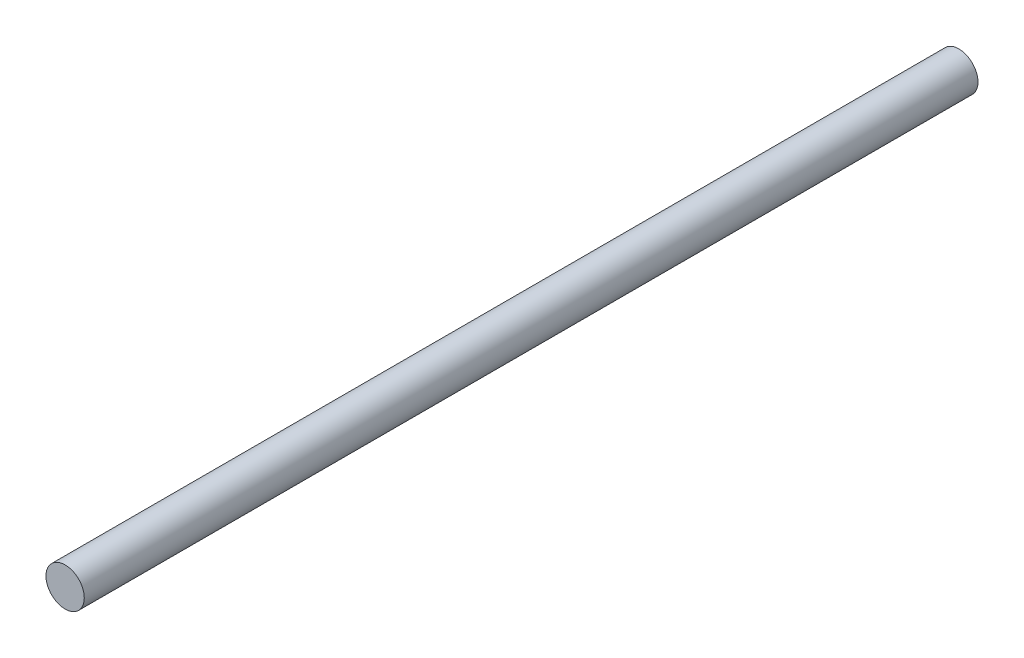
SolidWorks part; units mm, degrees
material "Plain Carbon Steel"
ref_plane "Front Plane" through (0, 0, 0) normal (0, 0, 1) x (1, 0, 0)
ref_plane "Top Plane" through (0, 0, 0) normal (0, 1, 0) x (1, 0, 0)
ref_plane "Right Plane" through (0, 0, 0) normal (1, 0, 0) x (0, 0, -1)
sketch "Sketch1" plane through (0, 0, 0) normal (0, 0, 1) x (1, 0, 0)
  circle A0 centre (0, 0) radius 1.5
  dimension "D1" = 3
extrude "Boss-Extrude1" add sketch "Sketch1" along normal blind 70
